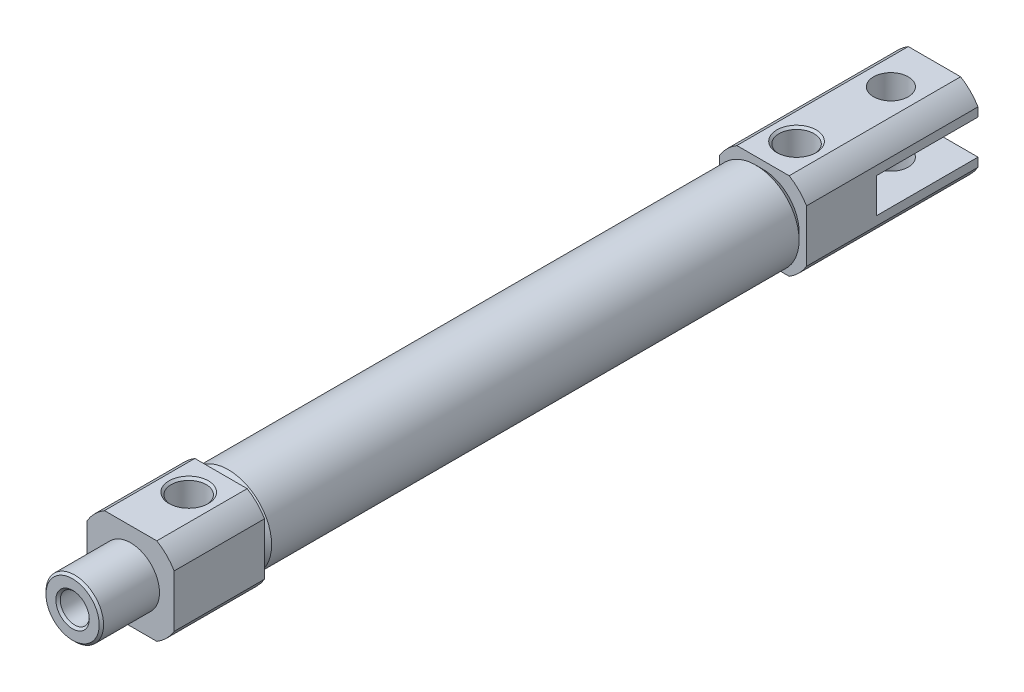
SolidWorks part; units mm, degrees
ref_plane "Front" through (0, 0, 0) normal (0, 0, 1) x (1, 0, 0)
ref_plane "Top" through (0, 0, 0) normal (0, 1, 0) x (1, 0, 0)
ref_plane "Right" through (0, 0, 0) normal (1, 0, 0) x (0, 0, -1)
sketch "Sketch1" plane through (0, 0, 0) normal (0, 0, 1) x (1, 0, 0)
  circle A0 centre (0, 0) radius 5.97
  dimension "D1" = 11.94
extrude "Base-Extrude" add sketch "Sketch1" along normal up to surface (37.335 mm away) and the other way up to surface (37.335 mm away)
chamfer "TubeChamfer" distance 1 angle 45 2 edges at (5.97, 0, 37.335) (5.97, 0, -37.335)
sketch "Sketch2" plane through (0, 0, 37.335) normal (0, 0, 1) x (1, 0, 0)
  line L1 (-3.6056, 6) -> (3.6056, 6)
  line L2 (-6, 3.6056) -> (-6, -3.6056)
  line L3 (-3.6056, -6) -> (3.6056, -6)
  line L4 (6, 3.6056) -> (6, -3.6056)
  arc A0 (6, 3.6056) -> (3.6056, 6) centre (0, 0) ccw
  arc A1 (3.6056, -6) -> (6, -3.6056) centre (0, 0) ccw
  arc A2 (-6, -3.6056) -> (-3.6056, -6) centre (0, 0) ccw
  arc A3 (-3.6056, 6) -> (-6, 3.6056) centre (0, 0) ccw
  point P4 (0, 5.6647)
  point P5 (-5.6647, 0)
  dimension "C" = 14
  dimension "B" = 12
extrude "RodCover" add sketch "Sketch2" along normal blind 12.45
sketch "Sketch3" plane through (0, 0, -37.335) normal (0, 0, -1) x (-1, 0, 0)
  line L1 (-3.6056, 6) -> (3.6056, 6)
  line L2 (-6, 3.6056) -> (-6, -3.6056)
  line L3 (-3.6056, -6) -> (3.6056, -6)
  line L4 (6, 3.6056) -> (6, -3.6056)
  arc A0 (-3.6056, 6) -> (-6, 3.6056) centre (0, 0) ccw
  arc A1 (-6, -3.6056) -> (-3.6056, -6) centre (0, 0) ccw
  arc A2 (3.6056, -6) -> (6, -3.6056) centre (0, 0) ccw
  arc A3 (6, 3.6056) -> (3.6056, 6) centre (0, 0) ccw
  point P1 (-6, 0)
  point P10 (0, 6)
  dimension "C Or 9" = 14
  dimension "B Or 8" = 12
extrude "HeadCover" add sketch "Sketch3" along normal blind 23.62
sketch "Sketch4" plane through (0, 0, 49.785) normal (0, 0, 1) x (1, 0, 0)
  circle A0 centre (0, 0) radius 3.9688
  dimension "NN" = 7.9375
extrude "NoseThreads" add sketch "Sketch4" along normal blind 8
sketch "Sketch5" plane through (0, 0, 0) normal (0, 1, 0) x (1, 0, 0)
  line L0 (3.6056, -49.785) -> (-3.6056, -49.785) construction
  circle A0 centre (0, -41.785) radius 2.415
  dimension "D1" = 4.83
  dimension "GA or GA-T" = 8
extrude "FrontPort" cut sketch "Sketch5" along normal through all
sketch "Sketch7" plane through (0, 0, 0) normal (1, 0, 0) x (0, 0, -1)
  line L0 (41.955, 0) -> (41.955, 22.4987) construction
  line L1 (-36.335, 0) -> (36.335, 0) construction
  line L2 (-39.37, 0) -> (-44.2, 0) construction
  line L3 (-39.37, 0) -> (-44.2, 0) construction
  line L4 (60.955, 3.6056) -> (60.955, -3.6056) construction
  line L5 (41.955, 0) -> (44.37, 0)
  line L6 (44.37, 0) -> (44.37, 5.7)
  line L8 (44.37, 5.7) -> (44.67, 6)
  line L9 (60.955, 6) -> (37.335, 6) construction
  line L10 (44.67, 6) -> (41.955, 6)
  line L11 (41.955, 6) -> (41.955, 0)
  line L12 (44.37, 0) -> (39.54, 0) construction
  point P15 (41.955, 0)
  dimension "D1" = 45
  dimension "GB" = 19
  dimension "D2" = 0.3
revolve "RearTopPort" cut sketch "Sketch7" angle 360 about L0
sketch "Sketch8" plane through (0, 0, 0) normal (1, 0, 0) x (0, 0, -1)
  line L0 (0, 0) -> (70.4928, 0) construction
  line L1 (-36.335, 0) -> (36.335, 0) construction
  line L2 (60.955, 0) -> (60.955, 2.715)
  line L3 (60.955, 3.6056) -> (60.955, 6) construction
  line L4 (60.955, 2.715) -> (60.655, 2.415)
  line L5 (60.655, 2.415) -> (55.955, 2.415)
  line L6 (55.955, 2.415) -> (55.955, 0)
  line L7 (55.955, 0) -> (60.955, 0)
  line L8 (60.955, 3.6056) -> (60.955, -3.6056) construction
  dimension "D1" = 4.83
  dimension "D2" = 5
  dimension "D3" = 45
  dimension "D4" = 0.3
revolve "RearInLinePort" [suppressed] cut sketch "Sketch8" angle 360 about L0
sketch "Sketch9" plane through (0, 0, 49.785) normal (0, 0, 1) x (1, 0, 0)
  line L1 (-5.5, 2.1354) -> (-5.5, -2.1354)
  line L2 (-4.5993, -3.6954) -> (-0.9007, -5.8308)
  line L3 (0.9007, -5.8308) -> (4.5993, -3.6954)
  line L4 (5.5, -2.1354) -> (5.5, 2.1354)
  line L5 (4.5993, 3.6954) -> (0.9007, 5.8308)
  line L6 (-0.9007, 5.8308) -> (-4.5993, 3.6954)
  circle A0 centre (0, 0) radius 5.5 construction
  arc A1 (-4.5993, 3.6954) -> (-5.5, 2.1354) centre (0, 0) ccw
  arc A2 (-5.5, -2.1354) -> (-4.5993, -3.6954) centre (0, 0) ccw
  arc A3 (-0.9007, -5.8308) -> (0.9007, -5.8308) centre (0, 0) ccw
  arc A4 (4.5993, -3.6954) -> (5.5, -2.1354) centre (0, 0) ccw
  arc A5 (5.5, 2.1354) -> (4.5993, 3.6954) centre (0, 0) ccw
  arc A6 (0.9007, 5.8308) -> (-0.9007, 5.8308) centre (0, 0) ccw
  dimension "D2" = 11.8
  dimension "D1" = 11
extrude "6BoreDetail" [suppressed] add sketch "Sketch9" along normal blind 3
sketch "Sketch10" plane through (0, 0, 57.785) normal (0, 0, 1) x (1, 0, 0)
  circle A0 centre (0, 0) radius 2
  dimension "D" = 4
extrude "RodBore" cut sketch "Sketch10" against normal up to surface (85.685 mm away)
sketch "Sketch11" plane through (0, 0, -27.9) normal (0, 0, 1) x (1, 0, 0)
  circle A0 centre (0, 0) radius 5
  dimension "Bore" = 10
extrude "StrokeChamber" cut sketch "Sketch11" against normal up to surface (55.8 mm away)
sketch "Sketch13" plane through (0, 0, 0) normal (1, 0, 0) x (0, 0, -1)
  line L0 (60.955, 3.6056) -> (60.955, -3.6056) construction
  line L1 (60.955, 2.39) -> (46.985, 2.39)
  line L2 (60.955, 2.39) -> (60.955, -2.39)
  line L3 (60.955, -2.39) -> (46.985, -2.39)
  line L4 (46.985, 2.39) -> (46.985, -2.39)
  point P4 (60.955, 0)
  dimension "CX" = 4.78
  dimension "R+U" = 13.97
extrude "D-ClevisSideCut" cut sketch "Sketch13" against normal through all and the other way through all
sketch "Sketch12" plane through (0, 0, 0) normal (0, 1, 0) x (1, 0, 0)
  line L0 (0, -36.335) -> (0, 36.335) construction
  line L1 (-3.6056, 60.955) -> (3.6056, 60.955) construction
  circle A0 centre (0, 54.955) radius 2.39
  dimension "D" = 4.78
  dimension "R" = 6
chamfer "DetailChamfer" distance 0.3 angle 45 3 edges at (3.9688, 0, 57.785) (0, 6, 44.2) (2, 0, 57.785)
ref_plane "SwitchPlaneA" through (0, 0, 26.235) normal (0, 0, -1) x (-1, 0, 0)
ref_plane "SwitchPlaneB" through (0, 0, -26.335) normal (0, 0, 1) x (1, 0, 0)
extrude "Cut-Extrude1" cut sketch "Sketch12" against normal through all both and the other way through all
